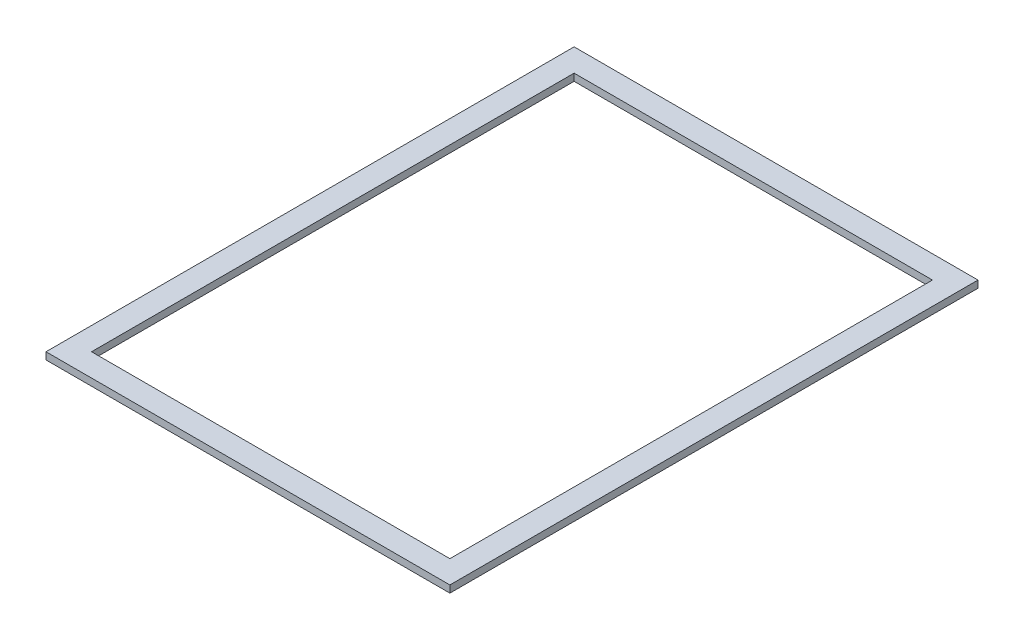
SolidWorks part; units mm, degrees
material "POLYURETHANE (11671)"
ref_plane "Front Plane" through (0, 0, 0) normal (0, 0, 1) x (1, 0, 0)
ref_plane "Top Plane" through (0, 0, 0) normal (0, 1, 0) x (1, 0, 0)
ref_plane "Right Plane" through (0, 0, 0) normal (1, 0, 0) x (0, 0, -1)
sketch "Sketch1" plane through (0, 129.032, 0) normal (0, 1, 0) x (1, 0, 0)
  line L0 (5.08, 112.748) -> (5.08, 5.08)
  line L1 (0, 117.828) -> (90.114, 117.828)
  line L2 (0, 117.828) -> (0, 0)
  line L3 (0, 0) -> (90.114, 0)
  line L4 (90.114, 117.828) -> (90.114, 0)
  line L5 (5.08, 5.08) -> (85.034, 5.08)
  line L6 (85.034, 112.748) -> (85.034, 5.08)
  line L7 (5.08, 112.748) -> (85.034, 112.748)
  dimension "D1" = 5.08
extrude "Boss-Extrude1" add sketch "Sketch1" along normal blind 1.5875
